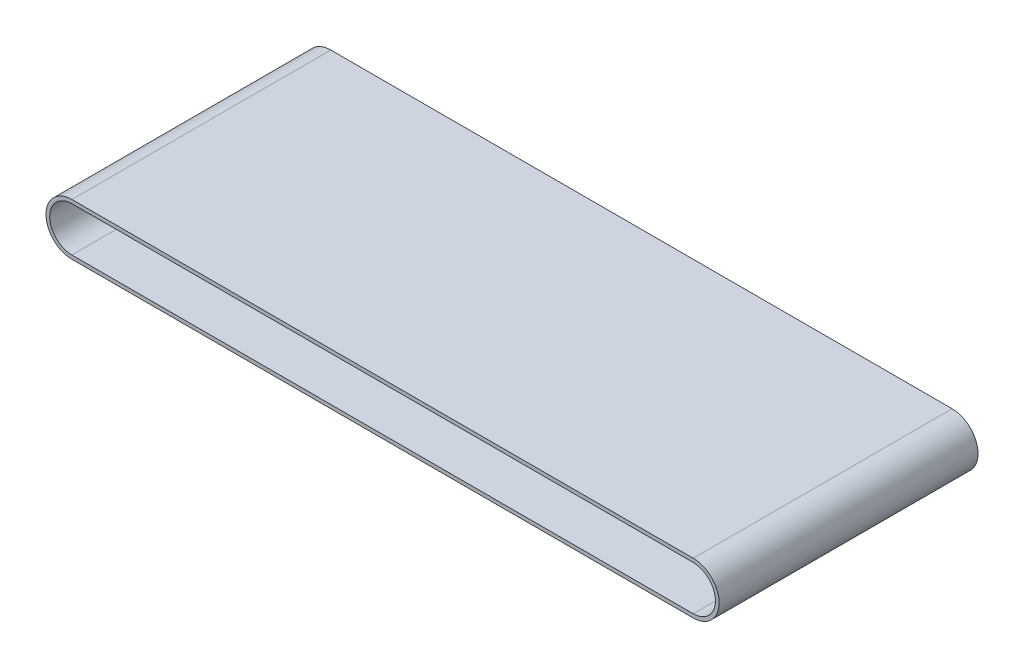
SolidWorks part; units mm, degrees
ref_plane "Front Plane" through (0, 0, 0) normal (0, 0, 1) x (1, 0, 0)
ref_plane "Top Plane" through (0, 0, 0) normal (0, 1, 0) x (1, 0, 0)
ref_plane "Right Plane" through (0, 0, 0) normal (1, 0, 0) x (0, 0, -1)
sketch "Sketch1" plane through (0, 0, 0) normal (0, 0, 1) x (1, 0, 0)
  line L1 (0, 44.45) -> (1066.8, 44.45)
  line L2 (0, -44.45) -> (1066.8, -44.45)
  arc A0 (0, 44.45) -> (0, -44.45) centre (0, 0) ccw
  arc A1 (1066.8, -44.45) -> (1066.8, 44.45) centre (1066.8, 0) ccw
  dimension "D1" = 88.9
  dimension "42" = 1066.8
extrude "Boss-Extrude1" add sketch "Sketch1" along normal mid plane 444.5
sketch "Sketch2" plane through (0, 0, -222.25) normal (0, 0, -1) x (-1, 0, 0)
  line L1 (-1066.8, 38.1) -> (0, 38.1)
  line L2 (0, -38.1) -> (-1066.8, -38.1)
  arc A0 (0, -38.1) -> (0, 38.1) centre (0, 0) ccw
  arc A1 (-1066.8, 38.1) -> (-1066.8, -38.1) centre (-1066.8, 0) ccw
  dimension "D2" = 76.2
  dimension "D3" = 76.2
  dimension "D1" = 1066.8
extrude "Cut-Extrude1" cut sketch "Sketch2" against normal through all both
